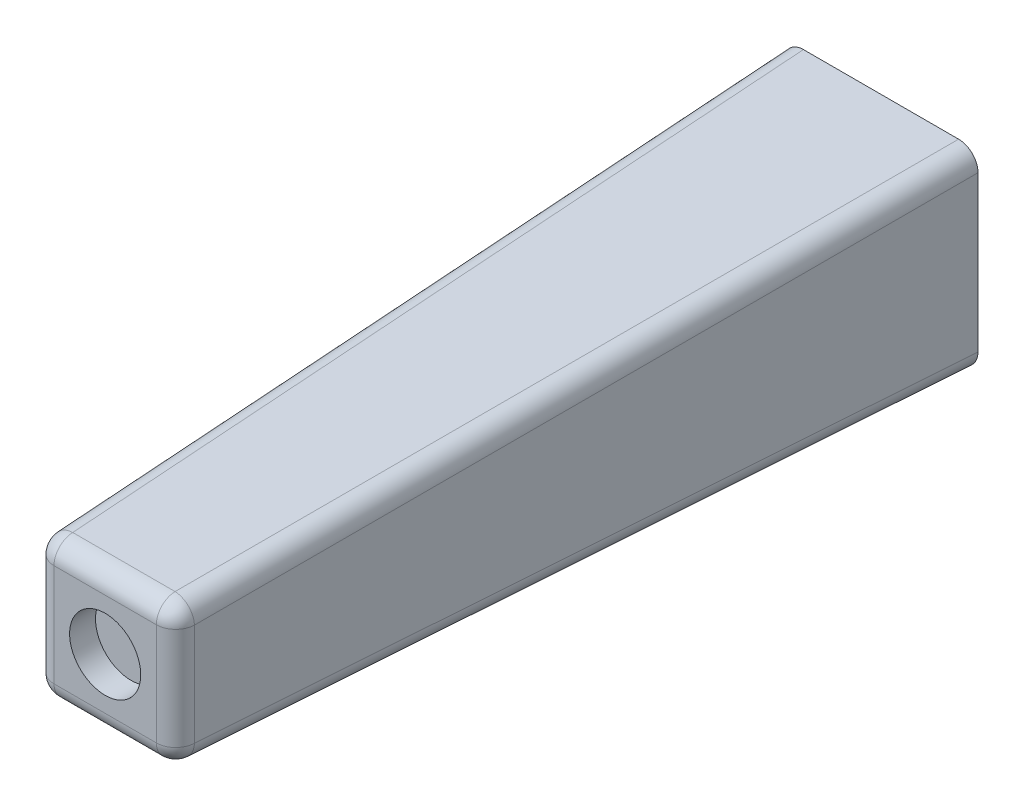
SolidWorks part; units mm, degrees
ref_plane "Спереди" through (0, 0, 0) normal (0, 0, 1) x (1, 0, 0)
ref_plane "Сверху" through (0, 0, 0) normal (0, 1, 0) x (1, 0, 0)
ref_plane "Справа" through (0, 0, 0) normal (1, 0, 0) x (0, 0, -1)
other "Configuration Table"
sketch "Sketch1" plane through (0, 0, 0) normal (0, 0, 1) x (1, 0, 0)
  line L1 (-7.5, -7.5) -> (7.5, -7.5)
  line L2 (-7.5, -7.5) -> (-7.5, 7.5)
  line L3 (-7.5, 7.5) -> (7.5, 7.5)
  line L4 (7.5, -7.5) -> (7.5, 7.5)
  line L5 (-7.5, -7.5) -> (7.5, 7.5) construction
  line L6 (-7.5, 7.5) -> (7.5, -7.5) construction
  point P0 (0, 0)
  point P8 (-7.5, 7.2307)
  point P10 (0, 0)
  point P11 (-6.3112, 7.8994)
  point P12 (0, 0)
  point P13 (5.5242, 7.9412)
  point P14 (7.3653, 7.3653)
  point P17 (-7.5, 5.2245)
  dimension "D1" = 15
  dimension "D2" = 15
extrude "Boss-Extrude1" add sketch "Sketch1" along normal blind 60 draft 2
sketch "Sketch2" plane through (0, 0, 0) normal (0, 0, -1) x (-1, 0, 0)
  circle A0 centre (0, 0) radius 1.5
  dimension "D1" = 3
extrude "Cut-Extrude1" cut sketch "Sketch2" against normal blind 10
sketch "Sketch3" plane through (0, 0, 60) normal (0, 0, 1) x (1, 0, 0)
  circle A0 centre (0, 0) radius 2.75
  dimension "D1" = 5.5
extrude "Cut-Extrude2" cut sketch "Sketch3" against normal blind 2
fillet "Fillet1" radius 1.5 8 edges at (0, 5.4048, 60) (5.4048, 0, 60) (0, -5.4048, 60) (-5.4048, 0, 60) (-6.4524, -6.4524, 30) (6.4524, 6.4524, 30) (-6.4524, 6.4524, 30) (6.4524, -6.4524, 30)
